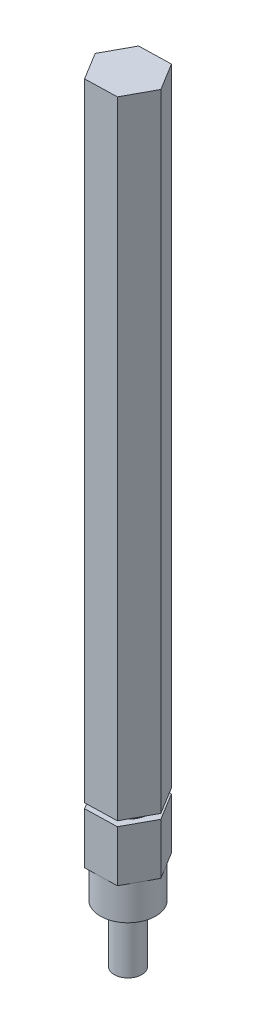
SolidWorks part; units mm, degrees
ref_plane "Front Plane" through (0, 0, 0) normal (0, 0, 1) x (1, 0, 0)
ref_plane "Top Plane" through (0, 0, 0) normal (0, 1, 0) x (1, 0, 0)
ref_plane "Right Plane" through (0, 0, 0) normal (1, 0, 0) x (0, 0, -1)
sketch "Sketch1" plane through (0, 0, 0) normal (0, 1, 0) x (1, 0, 0)
  circle A0 centre (0, 0) radius 3.1496
  dimension "D1" = 6.2992
extrude "Boss-Extrude1" add sketch "Sketch1" along normal blind 13.208
sketch "Sketch2" plane through (0, 13.208, 0) normal (0, 1, 0) x (1, 0, 0)
  circle A0 centre (0, 0) radius 6.35
  dimension "D1" = 12.7
extrude "Boss-Extrude2" add sketch "Sketch2" along normal blind 7.8867
sketch "Sketch3" plane through (0, 21.0947, 0) normal (0, 1, 0) x (1, 0, 0)
  line L1 (3.8286, -6.2534) -> (7.3299, 0.189)
  line L2 (7.3299, 0.189) -> (3.5013, 6.4424)
  line L3 (3.5013, 6.4424) -> (-3.8286, 6.2534)
  line L4 (-3.8286, 6.2534) -> (-7.3299, -0.189)
  line L5 (-7.3299, -0.189) -> (-3.5013, -6.4424)
  line L6 (-3.5013, -6.4424) -> (3.8286, -6.2534)
  circle A0 centre (0, 0) radius 6.35 construction
  dimension "D1" = 12.7
extrude "Boss-Extrude3" add sketch "Sketch3" along normal blind 11.7094
sketch "Sketch4" plane through (0, 32.8041, 0) normal (0, 1, 0) x (1, 0, 0)
  circle A0 centre (0, 0) radius 5.0292
  dimension "D1" = 10.0584
extrude "Boss-Extrude4" add sketch "Sketch4" along normal blind 1.1684
sketch "Sketch5" plane through (0, 33.9725, 0) normal (0, 1, 0) x (1, 0, 0)
  line L2 (-3.8286, 6.2534) -> (-7.3299, -0.189) construction
  line L3 (3.5013, 6.4424) -> (-3.8286, 6.2534) construction
  line L4 (7.3299, 0.189) -> (3.5013, 6.4424) construction
  line L5 (3.8286, -6.2534) -> (7.3299, 0.189) construction
  line L6 (-3.5013, -6.4424) -> (3.8286, -6.2534) construction
  line L9 (-7.3299, -0.189) -> (-3.5013, -6.4424) construction
  line L10 (-3.8286, 6.2534) -> (-7.3299, -0.189)
  line L11 (3.5013, 6.4424) -> (-3.8286, 6.2534)
  line L12 (7.3299, 0.189) -> (3.5013, 6.4424)
  line L13 (3.8286, -6.2534) -> (7.3299, 0.189)
  line L14 (-3.5013, -6.4424) -> (3.8286, -6.2534)
  line L15 (-7.3299, -0.189) -> (-3.5013, -6.4424)
extrude "Boss-Extrude5" add sketch "Sketch5" along normal blind 143.51
